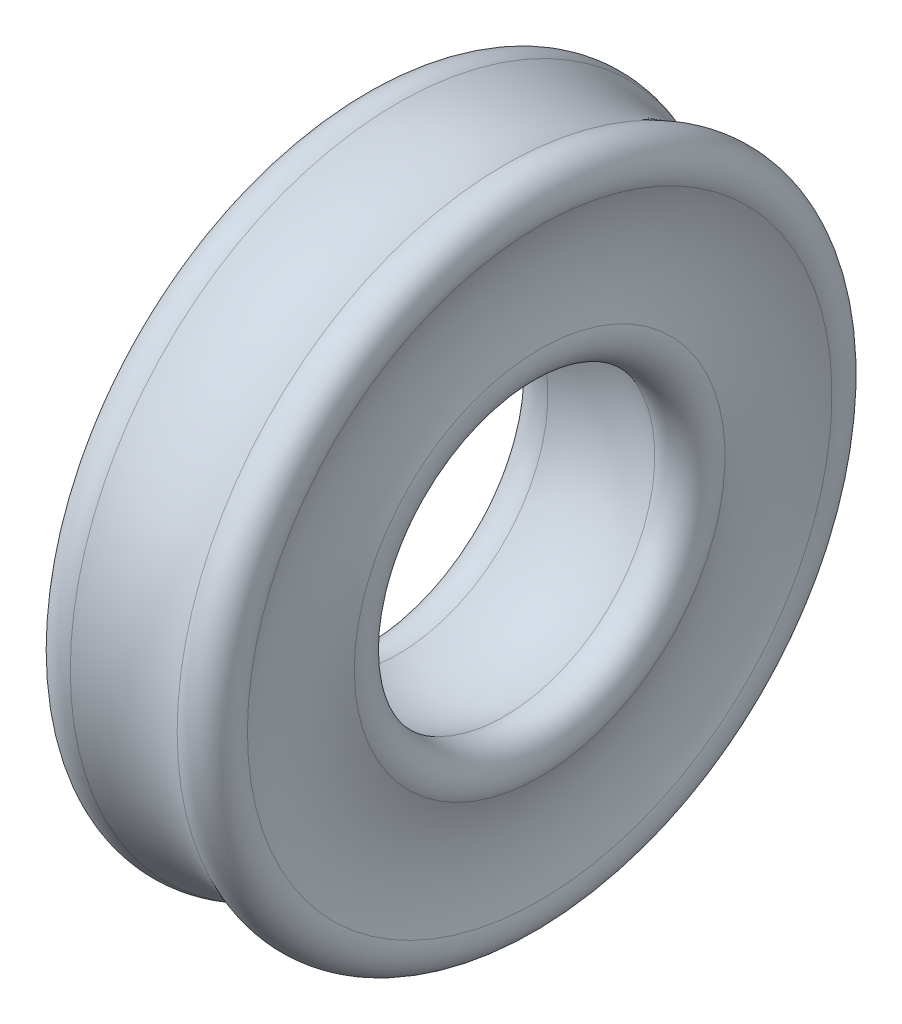
SolidWorks part; units mm, degrees
ref_plane "Front Plane" through (0, 0, 0) normal (0, 0, 1) x (1, 0, 0)
ref_plane "Top Plane" through (0, 0, 0) normal (0, 1, 0) x (1, 0, 0)
ref_plane "Right Plane" through (0, 0, 0) normal (1, 0, 0) x (0, 0, -1)
sketch "Sketch1" plane through (0, 0, 0) normal (0, 0, 1) x (1, 0, 0)
  line L0 (-0.889, 0) -> (0.889, 0) construction
  line L1 (-0.889, 3.2258) -> (0.889, 3.2258) construction
  line L2 (-0.889, 3.2258) -> (-0.889, 1.4478) construction
  line L3 (-0.889, 1.4478) -> (0.889, 1.4478) construction
  line L4 (0.889, 3.2258) -> (0.889, 1.4478) construction
  line L5 (-0.889, 1.4478) -> (0.889, 3.2258) construction
  line L9 (0.7557, 2.3368) -> (0.7557, 1.4478) construction
  line L11 (0.889, 1.4478) -> (0.889, -1.4478) construction
  line L12 (-0.889, 3.2258) -> (-0.889, -3.2258) construction
  circle A0 centre (0, 2.3368) radius 0.7557 construction
  arc A1 (-0.8666, 2.8597) -> (-0.8666, 1.8139) centre (-2.0436, 2.3368) cw
  arc A2 (-0.5229, 3.2034) -> (0.5229, 3.2034) centre (0, 4.3804) ccw
  arc A3 (-0.8666, 2.8597) -> (-0.5229, 3.2034) centre (-0.6286, 2.9654) cw
  arc A4 (0.8666, 2.8597) -> (0.8666, 1.8139) centre (2.0436, 2.3368) ccw
  arc A5 (-0.5229, 1.4702) -> (0.5229, 1.4702) centre (0, 0.2932) cw
  arc A6 (0.5229, 3.2034) -> (0.8666, 2.8597) centre (0.6286, 2.9654) cw
  arc A7 (-0.8666, 1.8139) -> (-0.5229, 1.4702) centre (-0.6286, 1.7082) ccw
  arc A8 (0.5229, 1.4702) -> (0.8666, 1.8139) centre (0.6286, 1.7082) ccw
  circle A9 centre (0, 2.3368) radius 0.889 construction
  dimension "D1" = 1.5113
revolve "Revolve1" add sketch "Sketch1" angle 360 mid plane about L0
equation "\"D1@Sketch1\" = \"Width@Sketch1\"*.85"
